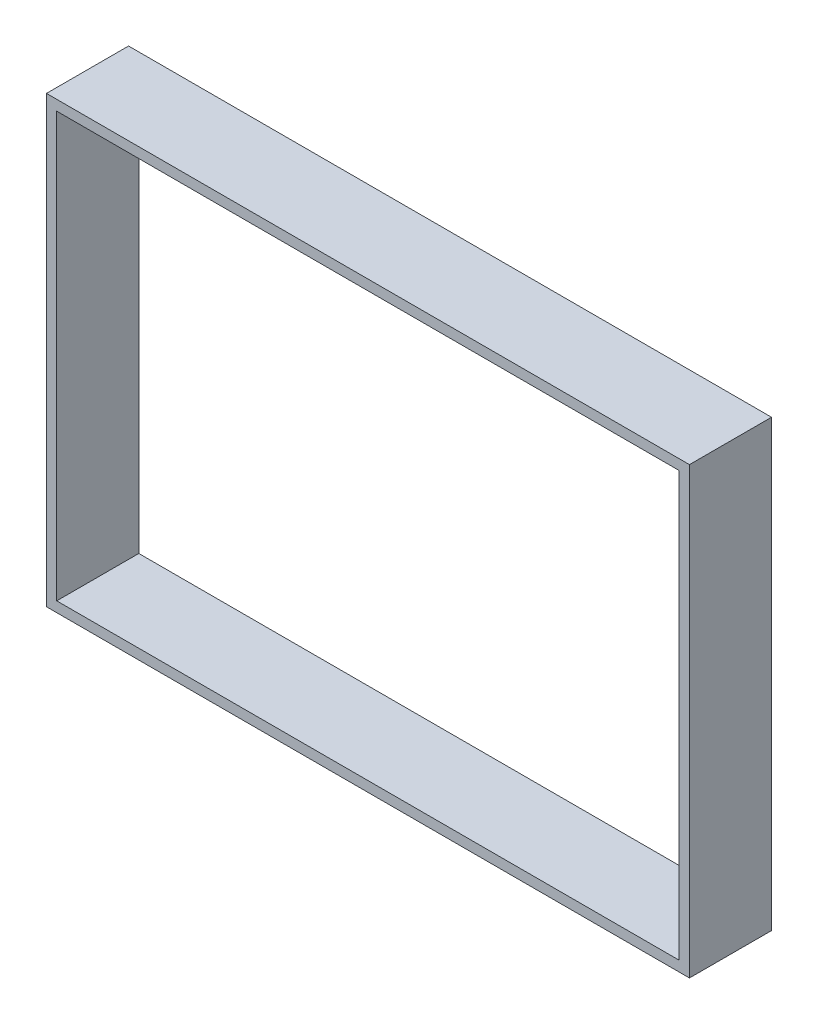
SolidWorks part; units mm, degrees
ref_plane "Front Plane" through (0, 0, 0) normal (0, 0, 1) x (1, 0, 0)
ref_plane "Top Plane" through (0, 0, 0) normal (0, 1, 0) x (1, 0, 0)
ref_plane "Right Plane" through (0, 0, 0) normal (1, 0, 0) x (0, 0, -1)
sketch "Sketch1" plane through (0, 0, 0) normal (0, 0, 1) x (1, 0, 0)
  line L4 (45.5, -31) -> (45.5, 31)
  line L5 (45.5, 31) -> (-45.5, 31)
  line L6 (-45.5, 31) -> (-45.5, -31)
  line L7 (-45.5, -31) -> (45.5, -31)
  line L8 (45.5, -31) -> (45.5, 31)
  line L9 (45.5, 31) -> (-45.5, 31)
  line L10 (-45.5, 31) -> (-45.5, -31)
  line L11 (-45.5, -31) -> (45.5, -31)
  line L12 (47, -32.5) -> (47, 32.5)
  line L13 (47, 32.5) -> (-47, 32.5)
  line L14 (-47, 32.5) -> (-47, -32.5)
  line L15 (-47, -32.5) -> (47, -32.5)
  line L16 (47, -32.5) -> (47, 32.5)
  line L17 (47, 32.5) -> (-47, 32.5)
  line L18 (-47, 32.5) -> (-47, -32.5)
  line L19 (-47, -32.5) -> (47, -32.5)
  dimension "D1" = 0
  dimension "D2" = 0
extrude "Top Walls" add sketch "Sketch1" along normal blind 12
